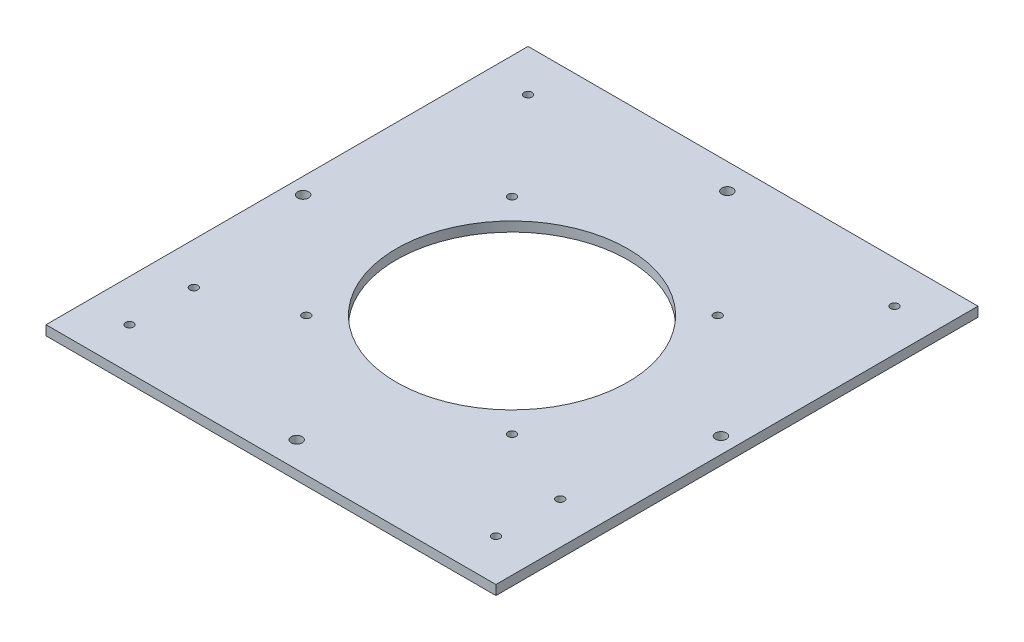
SolidWorks part; units mm, degrees
material "6061 合金"
ref_plane "前视基准面" through (0, 0, 0) normal (0, 0, 1) x (1, 0, 0)
ref_plane "上视基准面" through (0, 0, 0) normal (0, 1, 0) x (1, 0, 0)
ref_plane "右视基准面" through (0, 0, 0) normal (1, 0, 0) x (0, 0, -1)
sketch "草图1" plane through (0, 0, 0) normal (0, 0, 1) x (1, 0, 0)
  line L0 (12, 227.058) -> (152, 227.058)
  line L1 (12, 452.058) -> (12, 0) construction
  line L2 (152, 452.058) -> (152, 164.058) construction
  line L3 (152, 227.058) -> (12, 227.058) construction
extrude "拉伸-薄壁1" add sketch "草图1" along normal up to surface (150 mm away) thin contours L0
sketch "草图2" plane through (0, 224.058, 0) normal (0, -1, 0) x (1, 0, 0)
  circle A0 centre (82, 75) radius 36
  point P0 (82, 75)
  dimension "D1" = 72
extrude "切除-拉伸1" cut sketch "草图2" against normal up to next
sketch "草图3" plane through (0, 224.058, 0) normal (0, -1, 0) x (1, 0, 0)
  line L3 (82, 75) -> (82, 142) construction
  line L4 (50, 43) -> (114, 43) construction
  line L5 (50, 43) -> (50, 107) construction
  line L6 (50, 107) -> (114, 107) construction
  line L7 (114, 43) -> (114, 107) construction
  line L8 (50, 43) -> (114, 107) construction
  line L9 (50, 107) -> (114, 43) construction
  line L10 (152, 150) -> (12, 150) construction
  line L11 (82, 75) -> (147, 75) construction
  line L12 (82, 75) -> (82, 8) construction
  line L13 (82, 75) -> (17, 75) construction
  line L14 (152, 150) -> (152, 0) construction
  line L15 (25, 150) -> (25, 0) construction
  line L16 (139, 150) -> (139, 0) construction
  line L17 (25, 150) -> (25, 0)
  line L18 (139, 150) -> (139, 0)
  circle A0 centre (82, 75) radius 45.2548 construction
  circle A1 centre (82, 75) radius 50 construction
  point P17 (113.5104, 75)
  point P24 (139, 13)
  point P26 (25, 13)
  point P28 (25, 117)
  point P30 (25, 137)
  point P32 (139, 117)
  point P34 (139, 137)
  dimension "D3" = 100
  dimension "D1" = 64
  dimension "D2" = 64
  dimension "D4" = 8
  dimension "D5" = 5
hole_wizard "M3 螺纹孔的螺纹孔钻头1" positions "草图4" profile "草图5" hole size "M3" standard "GB" end condition through all
sketch "草图4" plane through (0, 224.058, 0) normal (0, -1, 0) x (-1, 0, 0)
  point P0 (-50, -107)
  point P3 (-50, -43)
  point P6 (-114, -43)
  point P9 (-114, -107)
sketch "草图5" plane through (50, 224.058, 107) normal (1, 0, 0) x (0, 0, -1)
  line L0 (0, 0) -> (0, 3)
  line L1 (0, 3) -> (1.25, 3)
  line L2 (1.25, 3) -> (1.25, 0)
  line L5 (1.25, 0) -> (0, 0)
  line L11 (0, -6.35) -> (0, 107.95) construction
  dimension "通孔孔直径" = 2.5
  dimension "通孔孔深度" = 3
hole_wizard "M3 间隙孔1" positions "草图6" profile "草图7" hole size "M3" standard "GB" end condition through all
sketch "草图6" plane through (0, 224.058, 0) normal (0, -1, 0) x (-1, 0, 0)
  point P0 (-82, -142)
  point P3 (-147, -75)
  point P6 (-82, -8)
  point P9 (-17, -75)
sketch "草图7" plane through (82, 224.058, 142) normal (1, 0, 0) x (0, 0, -1)
  line L0 (0, 0) -> (0, 3)
  line L1 (0, 3) -> (1.7, 3)
  line L2 (1.7, 3) -> (1.7, 0)
  line L5 (1.7, 0) -> (0, 0)
  line L11 (0, -6.35) -> (0, 107.95) construction
  dimension "通孔孔直径" = 3.4
  dimension "通孔孔深度" = 3
hole_wizard "M3 螺纹孔的螺纹孔钻头2" positions "草图8" profile "草图9" hole size "M3" standard "GB" end condition through all
sketch "草图8" plane through (0, 224.058, 0) normal (0, -1, 0) x (-1, 0, 0)
  point P0 (-139, -137)
  point P3 (-139, -117)
  point P6 (-139, -13)
  point P9 (-25, -137)
  point P12 (-25, -117)
  point P15 (-25, -13)
sketch "草图9" plane through (139, 224.058, 137) normal (1, 0, 0) x (0, 0, -1)
  line L0 (0, 0) -> (0, 3)
  line L1 (0, 3) -> (1.25, 3)
  line L2 (1.25, 3) -> (1.25, 0)
  line L5 (1.25, 0) -> (0, 0)
  line L11 (0, -6.35) -> (0, 107.95) construction
  dimension "通孔孔直径" = 2.5
  dimension "通孔孔深度" = 3
equation "\"D2@草图3\"=\"D1@草图3\""
